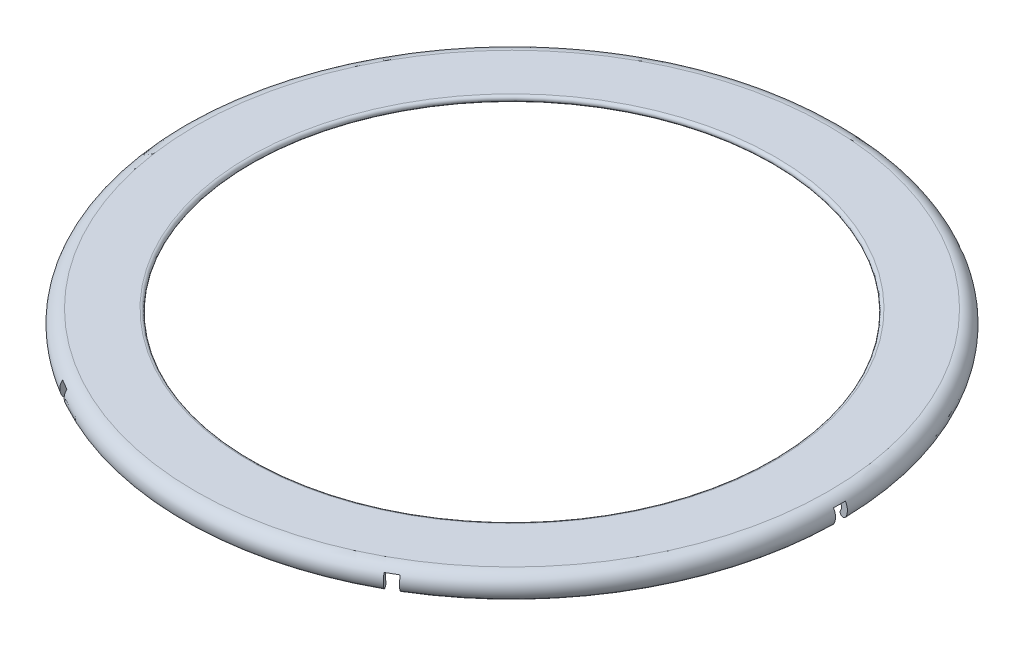
SolidWorks part; units mm, degrees
ref_plane "Front Plane" through (0, 0, 0) normal (0, 0, 1) x (1, 0, 0)
ref_plane "Top Plane" through (0, 0, 0) normal (0, 1, 0) x (1, 0, 0)
ref_plane "Right Plane" through (0, 0, 0) normal (1, 0, 0) x (0, 0, -1)
sketch "Sketch1" plane through (0, 0, 0) normal (0, 0, 1) x (1, 0, 0)
  line L1 (26.6647, 4) -> (-26.6647, 4) construction
  line L2 (-22.1647, 4.6) -> (-26.6647, 4.6)
  line L3 (-22.1647, 4) -> (-26.6647, 4) construction
  line L4 (-22.1647, 4.1) -> (-26.6647, 4.1)
  line L5 (-27.0977, 3.25) -> (-27.1843, 3.2) construction
  line L6 (-22.1647, 4) -> (-22.1647, 5.2432) construction
  line L7 (26.6647, 4) -> (-26.6647, 4) construction
  line L8 (26.6647, 4.1) -> (-26.6647, 4.1) construction
  line L9 (0, 0) -> (0, 13.9177) construction
  arc A0 (-26.6647, 4) -> (-26.7731, 3.0119) centre (-26.6647, 3.5) ccw construction
  arc A1 (-26.6647, 4) -> (-27.0977, 3.25) centre (-26.6647, 3.5) ccw construction
  arc A2 (-26.6647, 4.1) -> (-27.1843, 3.2) centre (-26.6647, 3.5) ccw
  arc A3 (-26.6647, 4) -> (-26.7731, 3.0119) centre (-26.6647, 3.5) ccw construction
  arc A4 (-26.6647, 4.1) -> (-26.7948, 2.9143) centre (-26.6647, 3.5) ccw construction
  arc A5 (-26.6647, 4.6) -> (-27.6173, 2.95) centre (-26.6647, 3.5) ccw
  arc A6 (-22.1647, 4.1) -> (-22.1647, 4.6) centre (-22.1647, 4.35) ccw
  arc A7 (-27.1843, 3.2) -> (-27.6173, 2.95) centre (-27.4008, 3.075) cw
  dimension "D4" = 4.5
  dimension "D2" = 30
  dimension "D1" = 0.1
  dimension "D3" = 0.5
revolve "Revolve1" add sketch "Sketch1" angle 360 about L9
sketch "Sketch2" plane through (0, 4.1, 0) normal (0, -1, 0) x (1, 0, 0)
  line L1 (-38.3812, 0.5) -> (38.3812, 0.5)
  line L2 (-38.3812, 0.5) -> (-38.3812, -0.5)
  line L3 (-38.3812, -0.5) -> (38.3812, -0.5)
  line L4 (38.3812, 0.5) -> (38.3812, -0.5)
  line L5 (-38.3812, 0.5) -> (38.3812, -0.5) construction
  line L6 (-38.3812, -0.5) -> (38.3812, 0.5) construction
  point P0 (0, 0)
  dimension "D1" = 1
extrude "Cut-Extrude1" cut sketch "Sketch2" along normal blind 11.684
pattern_circular "CirPattern1" count 3 over 360 about axis through (0, 0, 0) along (0, 1, 0) of "Cut-Extrude1"
